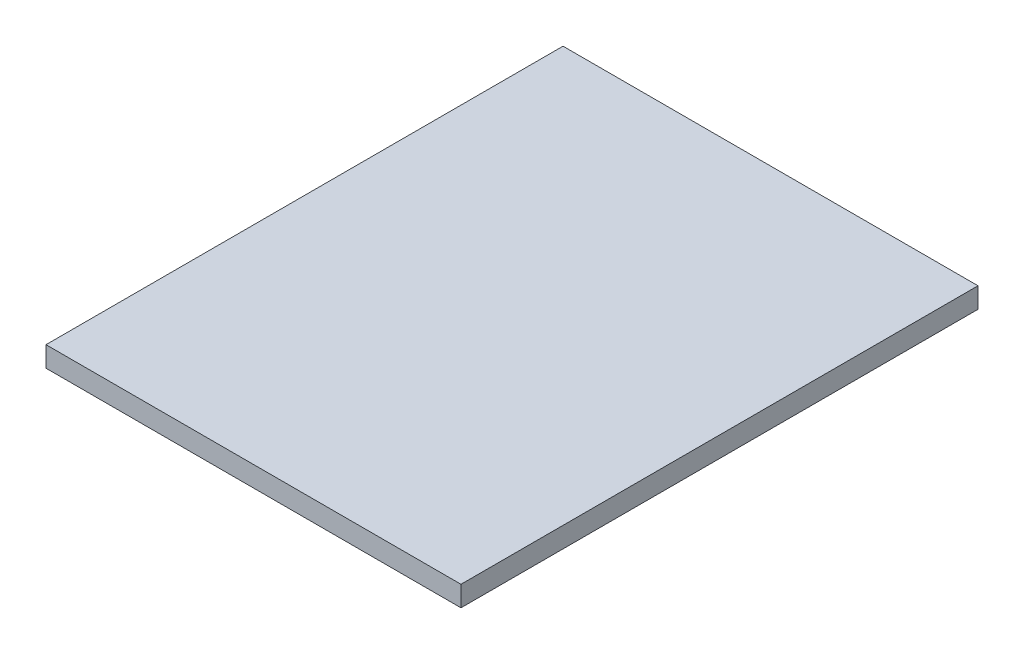
SolidWorks part; units mm, degrees
ref_plane "Front Plane" through (0, 0, 0) normal (0, 0, 1) x (1, 0, 0)
ref_plane "Top Plane" through (0, 0, 0) normal (0, 1, 0) x (1, 0, 0)
ref_plane "Right Plane" through (0, 0, 0) normal (1, 0, 0) x (0, 0, -1)
sketch "Sketch1" plane through (0, 0, 0) normal (0, 1, 0) x (1, 0, 0)
  line L1 (-96.8375, 120.65) -> (96.8375, 120.65)
  line L2 (-96.8375, 120.65) -> (-96.8375, -120.65)
  line L3 (-96.8375, -120.65) -> (96.8375, -120.65)
  line L4 (96.8375, 120.65) -> (96.8375, -120.65)
  line L5 (-96.8375, 120.65) -> (96.8375, -120.65) construction
  line L6 (-96.8375, -120.65) -> (96.8375, 120.65) construction
  point P0 (0, 0)
  dimension "D1" = 193.675
  dimension "D2" = 241.3
extrude "Boss-Extrude1" add sketch "Sketch1" along normal mid plane 9.525
